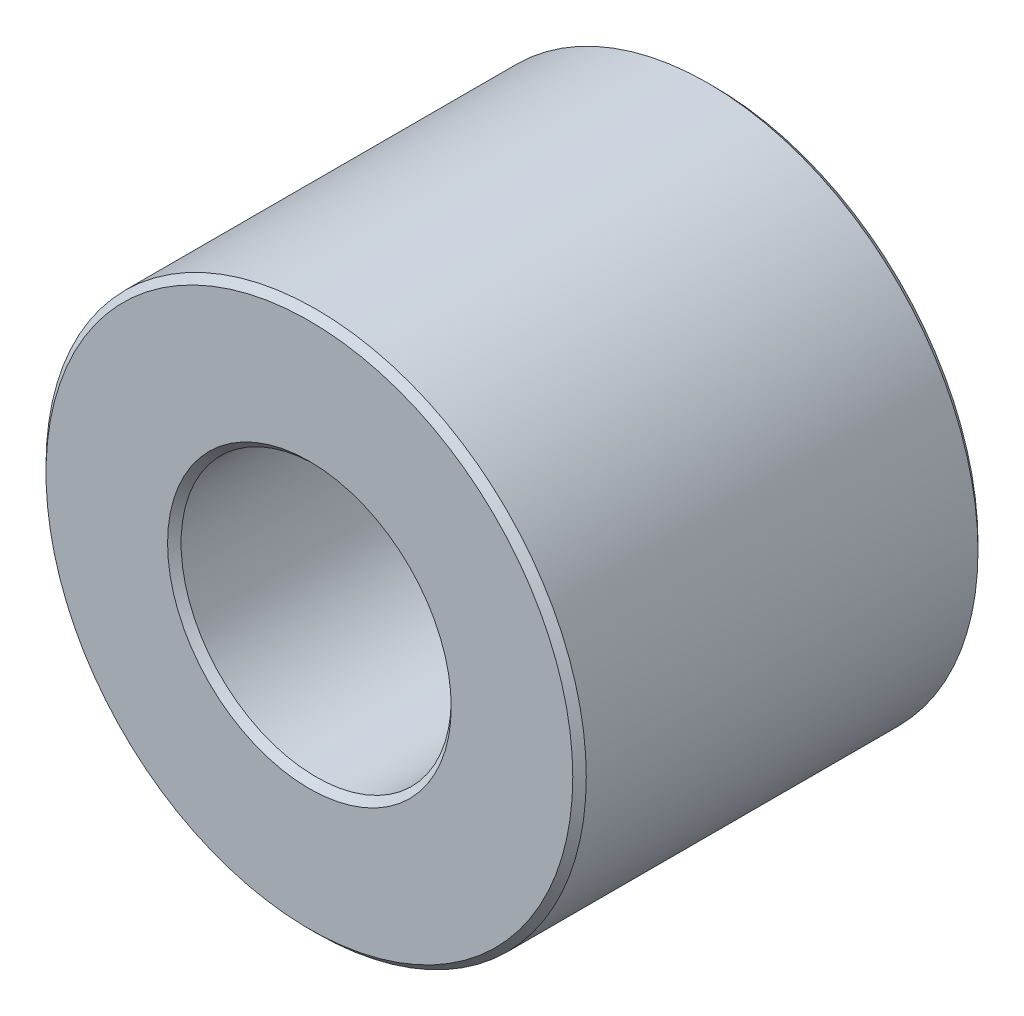
SolidWorks part; units mm, degrees
material "ABS"
ref_plane "Alzado" through (0, 0, 0) normal (0, 0, 1) x (1, 0, 0)
ref_plane "Planta" through (0, 0, 0) normal (0, 1, 0) x (1, 0, 0)
ref_plane "Vista lateral" through (0, 0, 0) normal (1, 0, 0) x (0, 0, -1)
sketch "Croquis1" plane through (0, 0, 0) normal (0, 0, 1) x (1, 0, 0)
  circle A0 centre (0, 0) radius 2
  circle A1 centre (0, 0) radius 4
  dimension "D1" = 4
  dimension "D2" = 8
extrude "Saliente-Extruir1" add sketch "Croquis1" along normal blind 6
chamfer "Chaflán1" distance 0.1 angle 45 4 edges at (2, 0, 0) (4, 0, 0) (4, 0, 6) (2, 0, 6)
